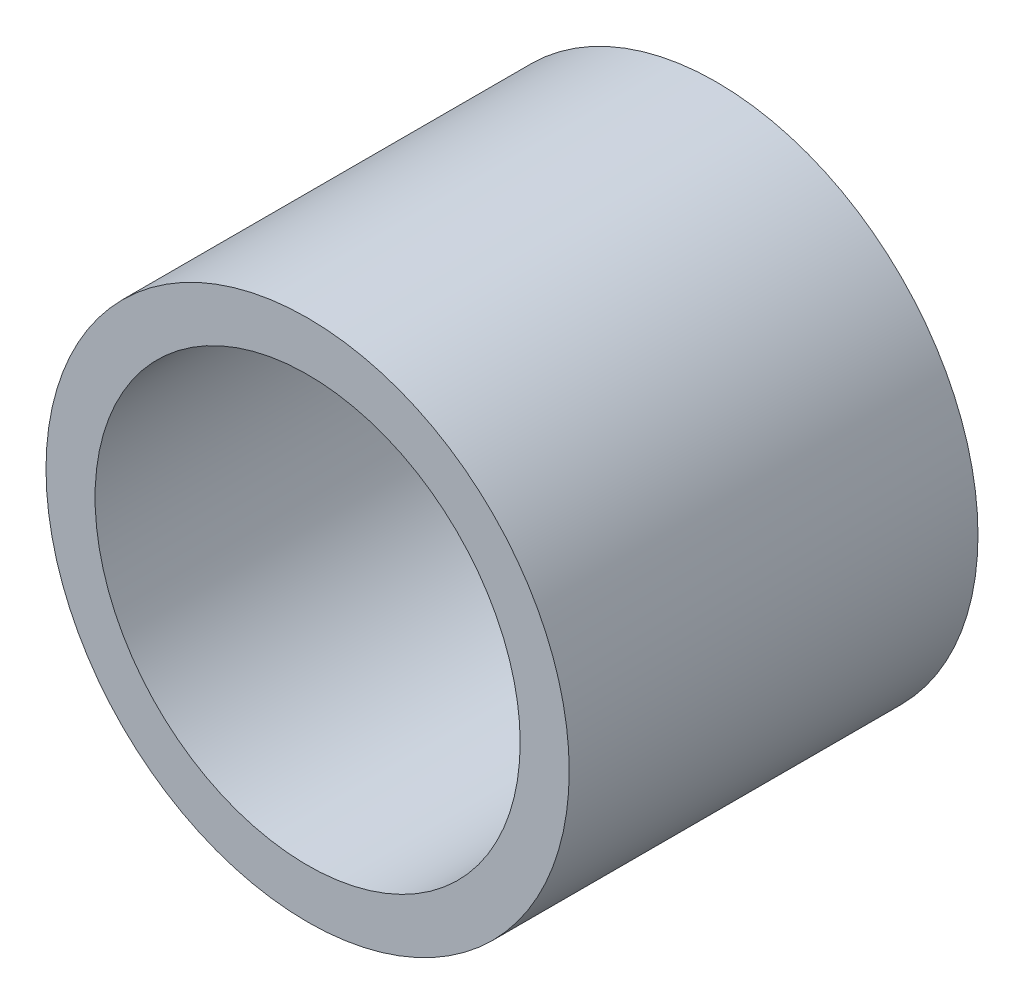
SolidWorks part; units mm, degrees
material "普通碳钢"
ref_plane "前视基准面" through (0, 0, 0) normal (0, 0, 1) x (1, 0, 0)
ref_plane "上视基准面" through (0, 0, 0) normal (0, 1, 0) x (1, 0, 0)
ref_plane "右视基准面" through (0, 0, 0) normal (1, 0, 0) x (0, 0, -1)
sketch "草图1" plane through (0, 0, 0) normal (0, 0, 1) x (1, 0, 0)
  circle A0 centre (0, 0) radius 13
  circle A1 centre (0, 0) radius 16
  dimension "D1" = 26
  dimension "D2" = 3
extrude "凸台-拉伸1" add sketch "草图1" along normal blind 25
